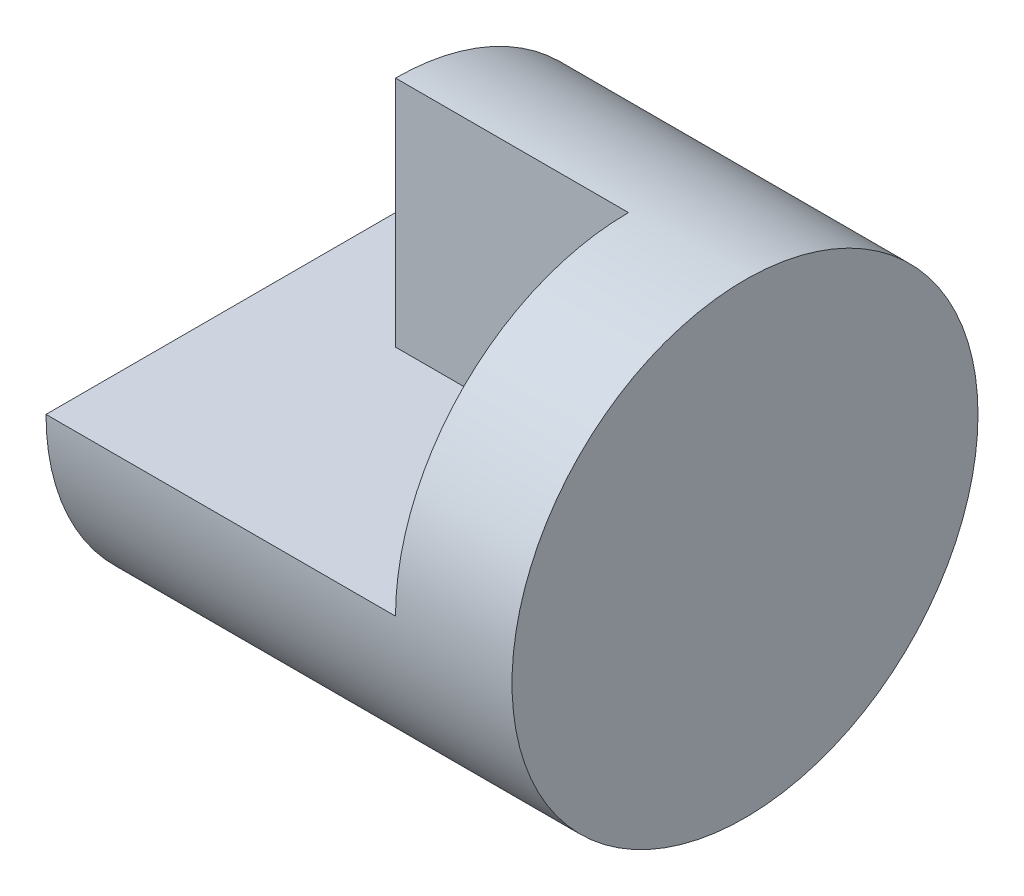
SolidWorks part; units mm, degrees
ref_plane "Front" through (0, 0, 0) normal (0, 0, 1) x (1, 0, 0)
ref_plane "Top" through (0, 0, 0) normal (0, 1, 0) x (1, 0, 0)
ref_plane "Right" through (0, 0, 0) normal (1, 0, 0) x (0, 0, -1)
sketch "Sketch1" plane through (0, 0, 0) normal (1, 0, 0) x (0, 0, -1)
  circle A0 centre (0, 0) radius 2
  dimension "D1" = 4
extrude "Boss-Extrude1" add sketch "Sketch1" along normal mid plane 4
sketch "Sketch3" plane through (0, 0, 0) normal (0, 1, 0) x (1, 0, 0)
  line L0 (-2, 2) -> (-2, -2)
  line L1 (-2, -2) -> (1, -2)
  line L2 (-2, -2) -> (2, -2) construction
  line L3 (1, -2) -> (1, 0)
  line L4 (1, 0) -> (-1, 0)
  line L5 (-1, 0) -> (-1, 2)
  line L6 (2, 2) -> (-2, 2) construction
  line L7 (-1, 2) -> (-2, 2)
  dimension "D1" = 1
  dimension "D2" = 3
  dimension "D3" = 2
extrude "Cut-Extrude1" cut sketch "Sketch3" along normal blind 4
